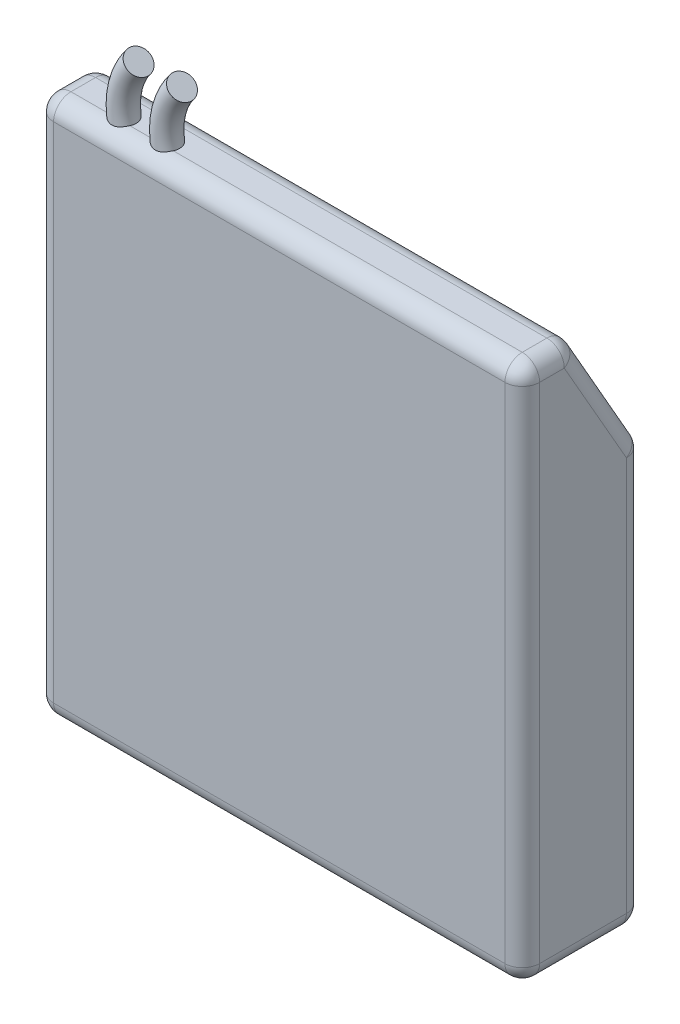
SolidWorks part; units mm, degrees
ref_plane "前视基准面" through (0, 0, 0) normal (0, 0, 1) x (1, 0, 0)
ref_plane "上视基准面" through (0, 0, 0) normal (0, 1, 0) x (1, 0, 0)
ref_plane "右视基准面" through (0, 0, 0) normal (1, 0, 0) x (0, 0, -1)
sketch "草图1" plane through (0, 0, 0) normal (1, 0, 0) x (0, 0, -1)
  line L0 (0, 0) -> (0, 31)
  line L1 (0, 31) -> (3, 31)
  line L2 (3, 31) -> (7, 24)
  line L3 (7, 24) -> (7, 0)
  line L4 (7, 0) -> (0, 0)
  dimension "D1" = 7
  dimension "D2" = 31
  dimension "D3" = 24
  dimension "D4" = 3
extrude "凸台-拉伸1" add sketch "草图1" along normal blind 28
fillet "圆角1" radius 1 15 edges at (14, 0, -7) (14, 24, -7) (14, 31, -3) (14, 31, 0) (14, 0, 0) (28, 15.5, 0) (28, 31, -1.5) (28, 27.5, -5) (28, 12, -7) (28, 0, -3.5) (0, 15.5, 0) (0, 31, -1.5) (0, 27.5, -5) (0, 12, -7) (0, 0, -3.5)
ref_plane "基准面1" through (0, 0, -1.3) normal (0, 0, 1) x (1, 0, 0)
sketch "草图2" plane through (0, 0, -1.3) normal (0, 0, 1) x (1, 0, 0)
  arc A0 (4.6475, 28.923) -> (4.597, 34.1426) centre (7.92, 31.5647) cw
sweep "扫描1" add path "草图2" circular profile diameter 1.4 parameters "D3"=1.4
pattern_linear "阵列(线性)1" count 2 spacing 2.5 along (1, 0, 0) of "扫描1"
